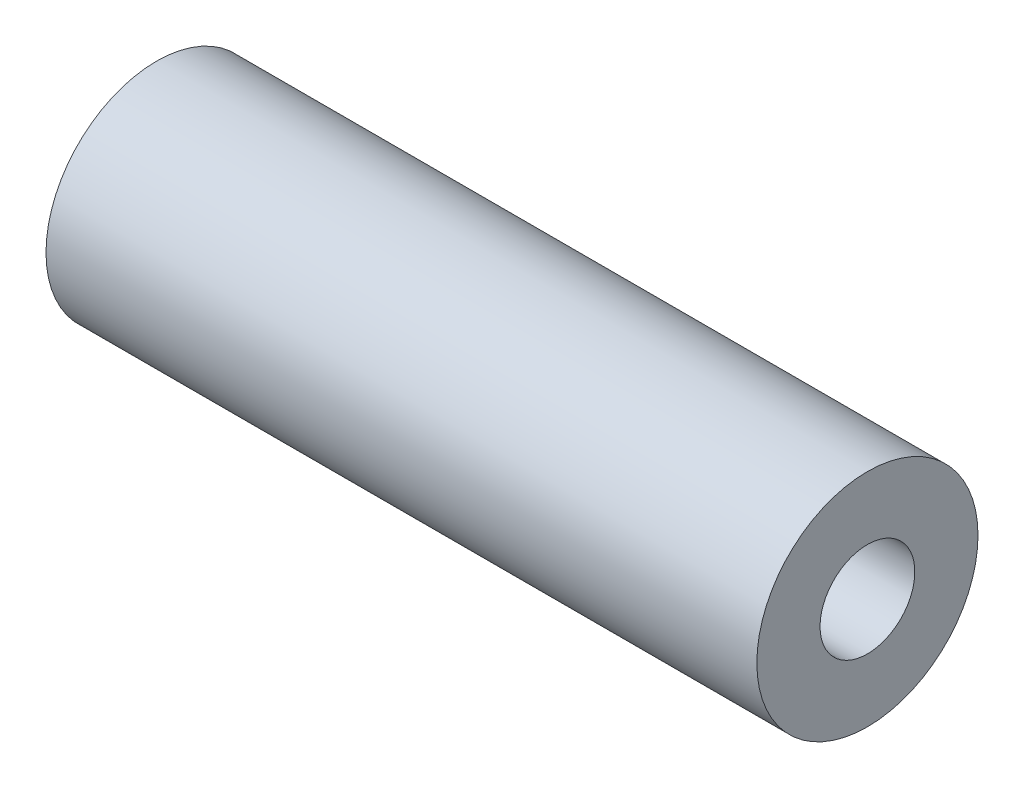
SolidWorks part; units mm, degrees
material "POM Acetal Copolymer"
ref_plane "Front Plane" through (0, 0, 0) normal (0, 0, 1) x (1, 0, 0)
ref_plane "Top Plane" through (0, 0, 0) normal (0, 1, 0) x (1, 0, 0)
ref_plane "Right Plane" through (0, 0, 0) normal (1, 0, 0) x (0, 0, -1)
sketch "Sketch1" plane through (0, 0, 0) normal (0, 0, 1) x (1, 0, 0)
  line L0 (-37.0032, 0) -> (22.5, 0) construction
  line L1 (-22.5, 7) -> (22.5, 7)
  line L2 (-22.5, 7) -> (-22.5, 3)
  line L3 (-22.5, 3) -> (22.5, 3)
  line L4 (22.5, 7) -> (22.5, 3)
  line L5 (22.5, 0) -> (22.5, 3) construction
  line L6 (0, 0) -> (0, 7) construction
  dimension "D1" = 6
  dimension "D2" = 45
  dimension "D3" = 14
revolve "Revolve1" add sketch "Sketch1" angle 360 about L0
